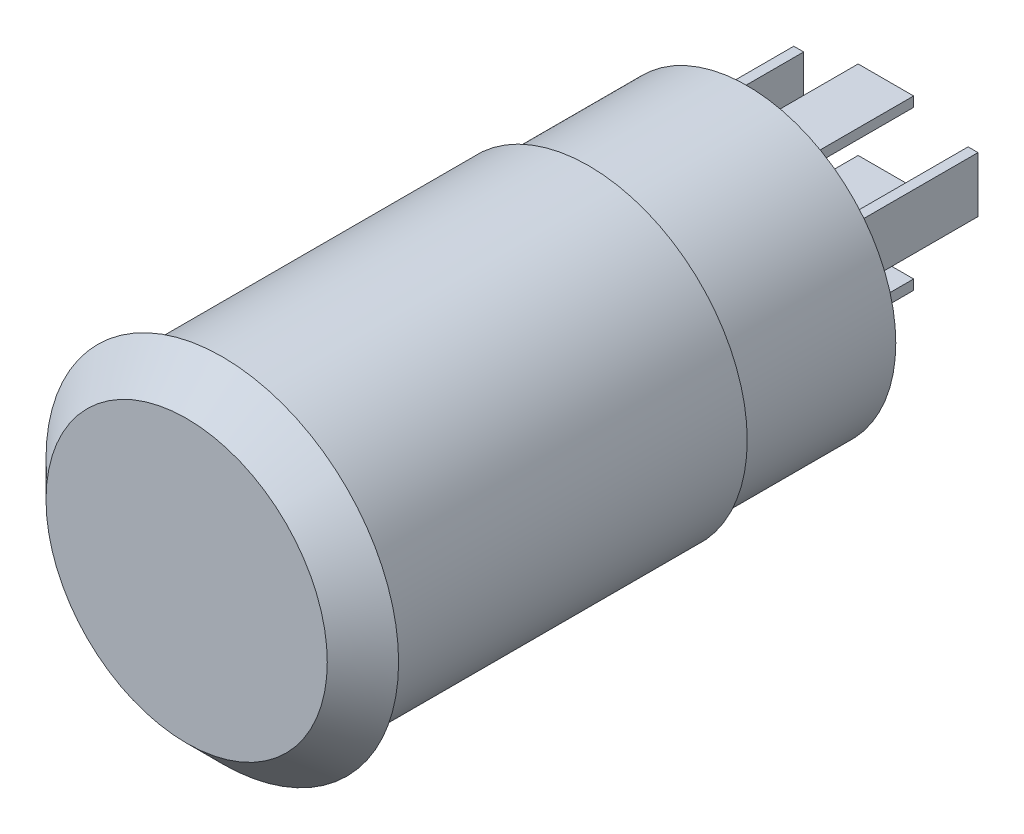
SolidWorks part; units mm, degrees
ref_plane "前视基准面" through (0, 0, 0) normal (0, 0, 1) x (1, 0, 0)
ref_plane "上视基准面" through (0, 0, 0) normal (0, 1, 0) x (1, 0, 0)
ref_plane "右视基准面" through (0, 0, 0) normal (1, 0, 0) x (0, 0, -1)
sketch "草图1" plane through (0, 0, 0) normal (0, 0, 1) x (1, 0, 0)
  circle A0 centre (0, 0) radius 8.9
  dimension "D1" = 17.8
extrude "凸台-拉伸1" add sketch "草图1" along normal blind 1.8 draft 45
sketch "草图2" plane through (0, 0, 0) normal (0, 0, -1) x (-1, 0, 0)
  circle A0 centre (0, 0) radius 8
  dimension "D1" = 16
extrude "凸台-拉伸2" add sketch "草图2" along normal blind 26.5
sketch "草图3" plane through (0, 0, -26.5) normal (0, 0, -1) x (-1, 0, 0)
  line L0 (-1.4, 0) -> (1.4, 0)
  line L1 (-1.4, 4) -> (1.4, 4)
  line L2 (-1.4, -4) -> (1.4, -4)
  line L3 (-4.4, 3.4) -> (-4.4, 0.6)
  line L4 (4.4, 3.4) -> (4.4, 0.6)
  point P4 (0, 0)
  point P12 (0, 0)
  dimension "D1" = 2.8
  dimension "D2" = 2.8
  dimension "D3" = 4
  dimension "D4" = 4
  dimension "D5" = 2.8
  dimension "D6" = 2.8
  dimension "D7" = 2.8
  dimension "D8" = 0.6
  dimension "D9" = 3
  dimension "D10" = 3
extrude "拉伸-薄壁1" add sketch "草图3" along normal blind 7 thin thin type mid plane wall 0.5
sketch "草图4" plane through (0, 0, -26.5) normal (0, 0, -1) x (-1, 0, 0)
  circle A0 centre (0, 0) radius 7.5
  dimension "D1" = 15
extrude "切除-拉伸-薄壁1" cut sketch "草图4" against normal blind 8 thin
